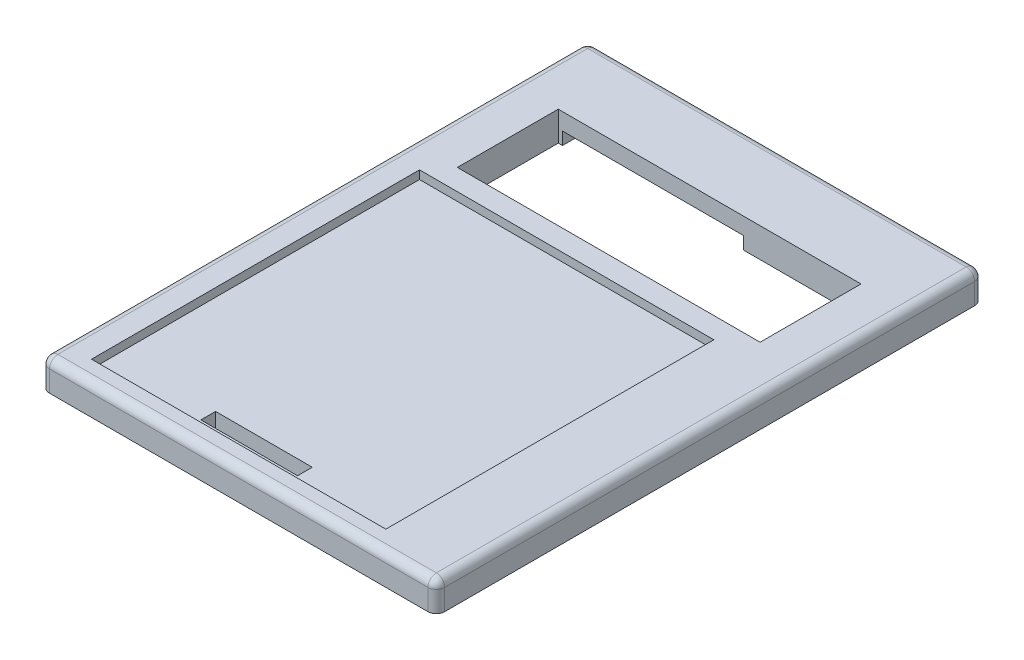
SolidWorks part; units mm, degrees
ref_plane "Front Plane" through (0, 0, 0) normal (0, 0, 1) x (1, 0, 0)
ref_plane "Top Plane" through (0, 0, 0) normal (0, 1, 0) x (1, 0, 0)
ref_plane "Right Plane" through (0, 0, 0) normal (1, 0, 0) x (0, 0, -1)
sketch "Sketch1" plane through (0, 0, 0) normal (0, 1, 0) x (1, 0, 0)
  line L1 (0, 0) -> (94, 0)
  line L2 (0, 0) -> (0, 130)
  line L3 (0, 130) -> (94, 130)
  line L4 (94, 0) -> (94, 130)
  dimension "D1" = 130
  dimension "D2" = 94
extrude "Boss-Extrude1" add sketch "Sketch1" along normal blind 7
sketch "Sketch2" plane through (0, 7, 0) normal (0, 1, 0) x (1, 0, 0)
  line L0 (94, 130) -> (0, 130) construction
  line L1 (11, 112) -> (83, 112)
  line L2 (11, 112) -> (11, 88)
  line L3 (11, 88) -> (83, 88)
  line L4 (83, 112) -> (83, 88)
  point P6 (47, 112)
  point P7 (47, 130)
  dimension "D1" = 72
  dimension "D2" = 24
  dimension "D3" = 18
extrude "Cut-Extrude1" cut sketch "Sketch2" against normal through all
sketch "Sketch3" plane through (0, 0, 0) normal (0, -1, 0) x (1, 0, 0)
  line L0 (83, -88) -> (83, -112) construction
  line L1 (89, -109) -> (83, -109)
  line L2 (89, -109) -> (89, -91)
  line L3 (89, -91) -> (83, -91)
  line L4 (83, -109) -> (83, -91)
  point P4 (83, -100)
  point P7 (83, -100)
  dimension "D1" = 6
  dimension "D2" = 18
extrude "Cut-Extrude2" cut sketch "Sketch3" against normal blind 3.5
sketch "Sketch4" plane through (0, 0, 0) normal (0, -1, 0) x (1, 0, 0)
  line L1 (55, -119.5) -> (12, -119.5)
  line L2 (55, -119.5) -> (55, -112)
  line L3 (55, -112) -> (12, -112)
  line L4 (12, -119.5) -> (12, -112)
  line L5 (83, -112) -> (11, -112) construction
  line L6 (0, -130) -> (0, 0) construction
  dimension "D1" = 43
  dimension "D2" = 7.5
  dimension "D3" = 12
extrude "Cut-Extrude3" cut sketch "Sketch4" against normal blind 3
sketch "Sketch5" plane through (0, 7, 0) normal (0, 1, 0) x (1, 0, 0)
  line L0 (0, 0) -> (94, 0) construction
  line L1 (7, 83) -> (77, 83)
  line L2 (7, 83) -> (7, 5)
  line L3 (7, 5) -> (77, 5)
  line L4 (77, 83) -> (77, 5)
  line L5 (0, 130) -> (0, 0) construction
  dimension "D1" = 78
  dimension "D2" = 70
  dimension "D3" = 5
  dimension "D4" = 7
extrude "Cut-Extrude4" cut sketch "Sketch5" against normal blind 2
sketch "Sketch6" plane through (0, 5, 0) normal (0, 1, 0) x (1, 0, 0)
  line L0 (7, 5) -> (77, 5) construction
  line L1 (30.5, 11) -> (53.5, 11)
  line L2 (30.5, 11) -> (30.5, 7.5)
  line L3 (30.5, 7.5) -> (53.5, 7.5)
  line L4 (53.5, 11) -> (53.5, 7.5)
  point P6 (42, 7.5)
  point P7 (42, 5)
  dimension "D1" = 23
  dimension "D2" = 3.5
  dimension "D3" = 2.5
extrude "Cut-Extrude5" cut sketch "Sketch6" against normal through all
fillet "Fillet1" radius 2 8 edges at (94, 3.5, -130) (0, 3.5, -130) (0, 3.5, 0) (94, 3.5, 0) (47, 7, 0) (94, 7, -65) (47, 7, -130) (0, 7, -65)
